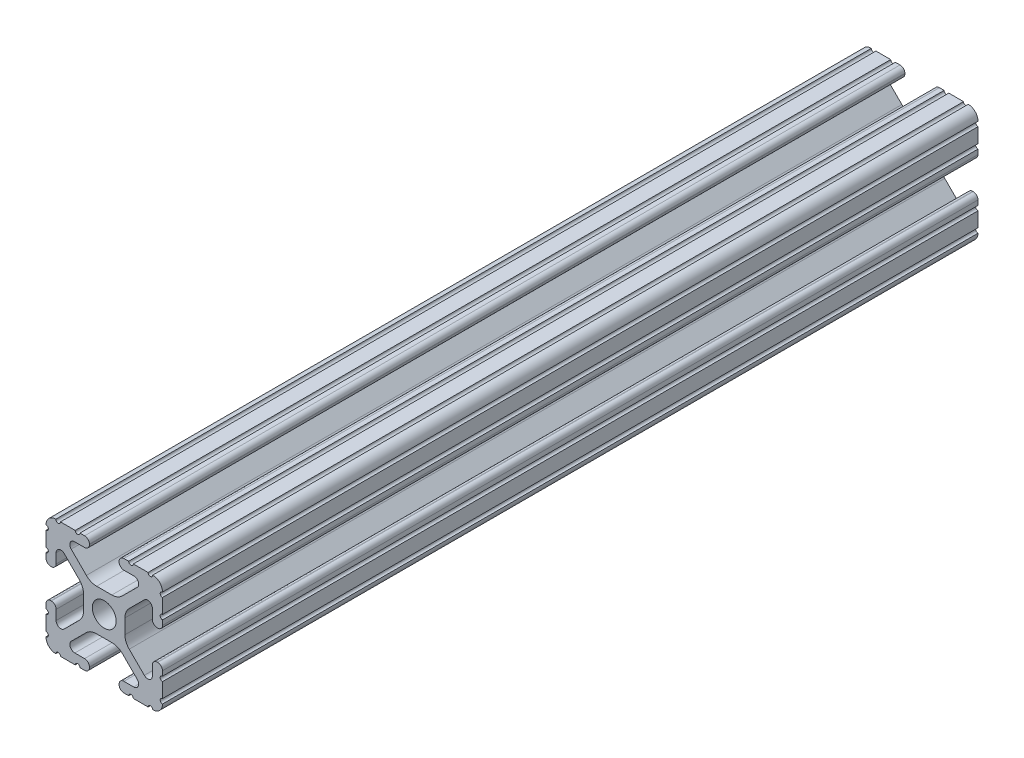
SolidWorks part; units mm, degrees
ref_plane "Front Plane" through (0, 0, 0) normal (0, 0, 1) x (1, 0, 0)
ref_plane "Top Plane" through (0, 0, 0) normal (0, 1, 0) x (1, 0, 0)
ref_plane "Right Plane" through (0, 0, 0) normal (1, 0, 0) x (0, 0, -1)
sketch "Sketch1" plane through (0, 0, 0) normal (0, 0, 1) x (1, 0, 0)
  line L0 (-1.7093, -4.4958) -> (1.7093, -4.4958)
  line L1 (3.9523, -5.4237) -> (7.1797, -8.6452)
  line L2 (6.4164, -10.4902) -> (4.2875, -10.4902)
  line L3 (3.2385, -11.5392) -> (3.2385, -11.651)
  line L4 (4.2875, -12.7) -> (5.3171, -12.7)
  line L5 (6.3331, -12.7) -> (9.5504, -12.7)
  line L6 (12.7, -9.5504) -> (12.7, -6.3331)
  line L7 (12.7, -5.3171) -> (12.7, -4.2875)
  line L8 (11.651, -3.2385) -> (11.5392, -3.2385)
  line L9 (10.4902, -4.2875) -> (10.4902, -6.4021)
  line L10 (8.7371, -7.1294) -> (5.441, -3.8408)
  line L11 (4.5085, -1.5932) -> (4.5085, 1.5932)
  line L12 (5.441, 3.8408) -> (8.7371, 7.1294)
  line L13 (10.4902, 6.4021) -> (10.4902, 4.2875)
  line L14 (11.5392, 3.2385) -> (11.651, 3.2385)
  line L15 (12.7, 4.2875) -> (12.7, 5.3171)
  line L16 (12.7, 6.3331) -> (12.7, 9.5504)
  line L17 (9.5504, 12.7) -> (6.3331, 12.7)
  line L18 (5.3171, 12.7) -> (4.2875, 12.7)
  line L19 (3.2385, 11.651) -> (3.2385, 11.5392)
  line L20 (4.2875, 10.4902) -> (6.4768, 10.4902)
  line L21 (7.207, 8.7244) -> (3.8983, 5.4232)
  line L22 (1.6558, 4.4958) -> (-1.6558, 4.4958)
  line L23 (-3.8983, 5.4232) -> (-7.207, 8.7244)
  line L24 (-6.4768, 10.4902) -> (-4.2875, 10.4902)
  line L25 (-3.2385, 11.5392) -> (-3.2385, 11.651)
  line L26 (-4.2875, 12.7) -> (-5.3171, 12.7)
  line L27 (-6.3331, 12.7) -> (-9.5504, 12.7)
  line L28 (-12.7, 9.5504) -> (-12.7, 6.3331)
  line L29 (-12.7, 5.3171) -> (-12.7, 4.2875)
  line L30 (-11.651, 3.2385) -> (-11.5392, 3.2385)
  line L31 (-10.4902, 4.2875) -> (-10.4902, 6.4021)
  line L32 (-8.7371, 7.1294) -> (-5.441, 3.8408)
  line L33 (-4.5085, 1.5932) -> (-4.5085, -1.5932)
  line L34 (-5.441, -3.8408) -> (-8.7371, -7.1294)
  line L35 (-10.4902, -6.4021) -> (-10.4902, -4.2875)
  line L36 (-11.5392, -3.2385) -> (-11.651, -3.2385)
  line L37 (-12.7, -4.2875) -> (-12.7, -5.3171)
  line L38 (-12.7, -6.3331) -> (-12.7, -9.5504)
  line L39 (-9.5504, -12.7) -> (-6.3331, -12.7)
  line L40 (-5.3171, -12.7) -> (-4.2875, -12.7)
  line L41 (-3.2385, -11.651) -> (-3.2385, -11.5392)
  line L42 (-4.2875, -10.4902) -> (-6.4164, -10.4902)
  line L43 (-7.1797, -8.6452) -> (-3.9523, -5.4237)
  line L44 (0, 0) -> (0, 2.5)
  line L45 (0, 0) -> (-2.5, 0)
  line L46 (0, 0) -> (0, -2.5)
  line L47 (0, 0) -> (2.5, 0)
  line L48 (0, 5) -> (0, 5.1035)
  line L49 (-5, 0) -> (-5.1035, 0)
  line L50 (0, -5) -> (0, -5.1035)
  line L51 (5, 0) -> (5.1035, 0)
  line L101 (-115.9492, 3668.6391) -> (-116.9788, 3668.6391)
  line L103 (-114.9001, 3668.6391) -> (-115.9492, 3668.6391)
  line L107 (-122.2281, 3668.6391) -> (-124.3615, 3668.6391)
  line L111 (-98.9618, 3668.6391) -> (-101.0952, 3668.6391)
  line L116 (-121.2121, 3668.6391) -> (-122.2281, 3668.6391)
  line L119 (-106.3445, 3668.6391) -> (-107.3741, 3668.6391)
  line L122 (-117.9948, 3668.6391) -> (-121.2121, 3668.6391)
  line L124 (-116.9788, 3668.6391) -> (-117.9948, 3668.6391)
  line L127 (-101.0952, 3668.6391) -> (-102.1112, 3668.6391)
  line L130 (-105.3285, 3668.6391) -> (-106.3445, 3668.6391)
  line L132 (-102.1112, 3668.6391) -> (-105.3285, 3668.6391)
  line L135 (-107.3741, 3668.6391) -> (-108.4231, 3668.6391)
  line L139 (-108.4231, 3668.6391) -> (-110.0059, 3668.6391)
  line L141 (-113.3174, 3668.6391) -> (-114.9001, 3668.6391)
  line L143 (-110.0059, 3668.6391) -> (-113.3174, 3668.6391)
  circle A0 centre (0, 0) radius 2.6035
  arc A1 (3.9523, -5.4237) -> (1.7093, -4.4958) centre (1.7093, -7.6708) ccw
  arc A2 (6.4164, -10.4902) -> (7.1797, -8.6452) centre (6.4164, -9.4098) ccw
  arc A3 (4.2875, -10.4902) -> (3.2385, -11.5392) centre (4.2875, -11.5392) ccw
  arc A4 (3.2385, -11.651) -> (4.2875, -12.7) centre (4.2875, -11.651) ccw
  arc A5 (6.3331, -12.7) -> (5.3171, -12.7) centre (5.8251, -12.7) ccw
  arc A6 (10.5664, -12.6998) -> (9.5504, -12.7) centre (10.0584, -12.7) ccw
  arc A7 (10.5664, -12.6998) -> (12.6998, -10.5664) centre (10.5918, -10.5918) ccw
  arc A8 (12.7, -9.5504) -> (12.6998, -10.5664) centre (12.7, -10.0584) ccw
  arc A9 (12.7, -5.3171) -> (12.7, -6.3331) centre (12.7, -5.8251) ccw
  arc A10 (12.7, -4.2875) -> (11.651, -3.2385) centre (11.651, -4.2875) ccw
  arc A11 (11.5392, -3.2385) -> (10.4902, -4.2875) centre (11.5392, -4.2875) ccw
  arc A12 (8.7371, -7.1294) -> (10.4902, -6.4021) centre (9.4628, -6.4021) ccw
  arc A13 (4.5085, -1.5932) -> (5.441, -3.8408) centre (7.6835, -1.5932) ccw
  arc A14 (5.441, 3.8408) -> (4.5085, 1.5932) centre (7.6835, 1.5932) ccw
  arc A15 (10.4902, 6.4021) -> (8.7371, 7.1294) centre (9.4628, 6.4021) ccw
  arc A16 (10.4902, 4.2875) -> (11.5392, 3.2385) centre (11.5392, 4.2875) ccw
  arc A17 (11.651, 3.2385) -> (12.7, 4.2875) centre (11.651, 4.2875) ccw
  arc A18 (12.7, 6.3331) -> (12.7, 5.3171) centre (12.7, 5.8251) ccw
  arc A19 (12.6998, 10.5664) -> (12.7, 9.5504) centre (12.7, 10.0584) ccw
  arc A20 (12.6998, 10.5664) -> (10.5664, 12.6998) centre (10.5918, 10.5918) ccw
  arc A21 (9.5504, 12.7) -> (10.5664, 12.6998) centre (10.0584, 12.7) ccw
  arc A22 (5.3171, 12.7) -> (6.3331, 12.7) centre (5.8251, 12.7) ccw
  arc A23 (4.2875, 12.7) -> (3.2385, 11.651) centre (4.2875, 11.651) ccw
  arc A24 (3.2385, 11.5392) -> (4.2875, 10.4902) centre (4.2875, 11.5392) ccw
  arc A25 (7.207, 8.7244) -> (6.4768, 10.4902) centre (6.4768, 9.4563) ccw
  arc A26 (1.6558, 4.4958) -> (3.8983, 5.4232) centre (1.6558, 7.6708) ccw
  arc A27 (-3.8983, 5.4232) -> (-1.6558, 4.4958) centre (-1.6558, 7.6708) ccw
  arc A28 (-6.4768, 10.4902) -> (-7.207, 8.7244) centre (-6.4768, 9.4563) ccw
  arc A29 (-4.2875, 10.4902) -> (-3.2385, 11.5392) centre (-4.2875, 11.5392) ccw
  arc A30 (-3.2385, 11.651) -> (-4.2875, 12.7) centre (-4.2875, 11.651) ccw
  arc A31 (-6.3331, 12.7) -> (-5.3171, 12.7) centre (-5.8251, 12.7) ccw
  arc A32 (-10.5664, 12.6998) -> (-9.5504, 12.7) centre (-10.0584, 12.7) ccw
  arc A33 (-10.5664, 12.6998) -> (-12.6998, 10.5664) centre (-10.5918, 10.5918) ccw
  arc A34 (-12.7, 9.5504) -> (-12.6998, 10.5664) centre (-12.7, 10.0584) ccw
  arc A35 (-12.7, 5.3171) -> (-12.7, 6.3331) centre (-12.7, 5.8251) ccw
  arc A36 (-12.7, 4.2875) -> (-11.651, 3.2385) centre (-11.651, 4.2875) ccw
  arc A37 (-11.5392, 3.2385) -> (-10.4902, 4.2875) centre (-11.5392, 4.2875) ccw
  arc A38 (-8.7371, 7.1294) -> (-10.4902, 6.4021) centre (-9.4628, 6.4021) ccw
  arc A39 (-4.5085, 1.5932) -> (-5.441, 3.8408) centre (-7.6835, 1.5932) ccw
  arc A40 (-5.441, -3.8408) -> (-4.5085, -1.5932) centre (-7.6835, -1.5932) ccw
  arc A41 (-10.4902, -6.4021) -> (-8.7371, -7.1294) centre (-9.4628, -6.4021) ccw
  arc A42 (-10.4902, -4.2875) -> (-11.5392, -3.2385) centre (-11.5392, -4.2875) ccw
  arc A43 (-11.651, -3.2385) -> (-12.7, -4.2875) centre (-11.651, -4.2875) ccw
  arc A44 (-12.7, -6.3331) -> (-12.7, -5.3171) centre (-12.7, -5.8251) ccw
  arc A45 (-12.6998, -10.5664) -> (-12.7, -9.5504) centre (-12.7, -10.0584) ccw
  arc A46 (-12.6998, -10.5664) -> (-10.5664, -12.6998) centre (-10.5918, -10.5918) ccw
  arc A47 (-9.5504, -12.7) -> (-10.5664, -12.6998) centre (-10.0584, -12.7) ccw
  arc A48 (-5.3171, -12.7) -> (-6.3331, -12.7) centre (-5.8251, -12.7) ccw
  arc A49 (-4.2875, -12.7) -> (-3.2385, -11.651) centre (-4.2875, -11.651) ccw
  arc A50 (-3.2385, -11.5392) -> (-4.2875, -10.4902) centre (-4.2875, -11.5392) ccw
  arc A51 (-7.1797, -8.6452) -> (-6.4164, -10.4902) centre (-6.4164, -9.4098) ccw
  arc A52 (-1.7093, -4.4958) -> (-3.9523, -5.4237) centre (-1.7093, -7.6708) ccw
extrude "Boss-Extrude1" add sketch "Sketch1" along normal blind 2463.8 contours A52 L0 A1 L1 A2 L2 A3 L3 A4 L4 A5 L5 A6 A7 A8 L6 A9 L7 A10 L8 A11 L9 A12 L10 A13 L11 A14 L12 A15 L13 A16 L14 A17 L15 A18 L16 A19 A20 A21 L17 A22 L18 A23 L19 A24 L20 A25 L21 A26 L22 A27
sketch "Sketch2" plane through (0, 0, 2463.8) normal (0, 0, 1) x (1, 0, 0)
  line L44 (-1.7093, -4.4958) -> (1.7093, -4.4958)
  line L45 (3.9523, -5.4237) -> (7.1797, -8.6452)
  line L46 (6.4164, -10.4902) -> (4.2875, -10.4902)
  line L47 (3.2385, -11.5392) -> (3.2385, -11.651)
  line L48 (4.2875, -12.7) -> (5.3171, -12.7)
  line L49 (6.3331, -12.7) -> (9.5504, -12.7)
  line L50 (12.7, -9.5504) -> (12.7, -6.3331)
  line L51 (12.7, -5.3171) -> (12.7, -4.2875)
  line L52 (11.651, -3.2385) -> (11.5392, -3.2385)
  line L53 (10.4902, -4.2875) -> (10.4902, -6.4021)
  line L54 (8.7371, -7.1294) -> (5.441, -3.8408)
  line L55 (4.5085, -1.5932) -> (4.5085, 1.5932)
  line L56 (5.441, 3.8408) -> (8.7371, 7.1294)
  line L57 (10.4902, 6.4021) -> (10.4902, 4.2875)
  line L58 (11.5392, 3.2385) -> (11.651, 3.2385)
  line L59 (12.7, 4.2875) -> (12.7, 5.3171)
  line L60 (12.7, 6.3331) -> (12.7, 9.5504)
  line L61 (9.5504, 12.7) -> (6.3331, 12.7)
  line L62 (5.3171, 12.7) -> (4.2875, 12.7)
  line L63 (3.2385, 11.651) -> (3.2385, 11.5392)
  line L64 (4.2875, 10.4902) -> (6.4768, 10.4902)
  line L65 (7.207, 8.7244) -> (3.8983, 5.4232)
  line L66 (1.6558, 4.4958) -> (-1.6558, 4.4958)
  line L67 (-3.8983, 5.4232) -> (-7.207, 8.7244)
  line L68 (-6.4768, 10.4902) -> (-4.2875, 10.4902)
  line L69 (-3.2385, 11.5392) -> (-3.2385, 11.651)
  line L70 (-4.2875, 12.7) -> (-5.3171, 12.7)
  line L71 (-6.3331, 12.7) -> (-9.5504, 12.7)
  line L72 (-12.7, 9.5504) -> (-12.7, 6.3331)
  line L73 (-12.7, 5.3171) -> (-12.7, 4.2875)
  line L74 (-11.651, 3.2385) -> (-11.5392, 3.2385)
  line L75 (-10.4902, 4.2875) -> (-10.4902, 6.4021)
  line L76 (-8.7371, 7.1294) -> (-5.441, 3.8408)
  line L77 (-4.5085, 1.5932) -> (-4.5085, -1.5932)
  line L78 (-5.441, -3.8408) -> (-8.7371, -7.1294)
  line L79 (-10.4902, -6.4021) -> (-10.4902, -4.2875)
  line L80 (-11.5392, -3.2385) -> (-11.651, -3.2385)
  line L81 (-12.7, -4.2875) -> (-12.7, -5.3171)
  line L82 (-12.7, -6.3331) -> (-12.7, -9.5504)
  line L83 (-9.5504, -12.7) -> (-6.3331, -12.7)
  line L84 (-5.3171, -12.7) -> (-4.2875, -12.7)
  line L85 (-3.2385, -11.651) -> (-3.2385, -11.5392)
  line L86 (-4.2875, -10.4902) -> (-6.4164, -10.4902)
  line L87 (-7.1797, -8.6452) -> (-3.9523, -5.4237)
  line L88 (-1.7093, -4.4958) -> (1.7093, -4.4958)
  line L89 (3.9523, -5.4237) -> (7.1797, -8.6452)
  line L90 (6.4164, -10.4902) -> (4.2875, -10.4902)
  line L91 (3.2385, -11.5392) -> (3.2385, -11.651)
  line L92 (4.2875, -12.7) -> (5.3171, -12.7)
  line L93 (6.3331, -12.7) -> (9.5504, -12.7)
  line L94 (12.7, -9.5504) -> (12.7, -6.3331)
  line L95 (12.7, -5.3171) -> (12.7, -4.2875)
  line L96 (11.651, -3.2385) -> (11.5392, -3.2385)
  line L97 (10.4902, -4.2875) -> (10.4902, -6.4021)
  line L98 (8.7371, -7.1294) -> (5.441, -3.8408)
  line L99 (4.5085, -1.5932) -> (4.5085, 1.5932)
  line L100 (5.441, 3.8408) -> (8.7371, 7.1294)
  line L101 (10.4902, 6.4021) -> (10.4902, 4.2875)
  line L102 (11.5392, 3.2385) -> (11.651, 3.2385)
  line L103 (12.7, 4.2875) -> (12.7, 5.3171)
  line L104 (12.7, 6.3331) -> (12.7, 9.5504)
  line L105 (9.5504, 12.7) -> (6.3331, 12.7)
  line L106 (5.3171, 12.7) -> (4.2875, 12.7)
  line L107 (3.2385, 11.651) -> (3.2385, 11.5392)
  line L108 (4.2875, 10.4902) -> (6.4768, 10.4902)
  line L109 (7.207, 8.7244) -> (3.8983, 5.4232)
  line L110 (1.6558, 4.4958) -> (-1.6558, 4.4958)
  line L111 (-3.8983, 5.4232) -> (-7.207, 8.7244)
  line L112 (-6.4768, 10.4902) -> (-4.2875, 10.4902)
  line L113 (-3.2385, 11.5392) -> (-3.2385, 11.651)
  line L114 (-4.2875, 12.7) -> (-5.3171, 12.7)
  line L115 (-6.3331, 12.7) -> (-9.5504, 12.7)
  line L116 (-12.7, 9.5504) -> (-12.7, 6.3331)
  line L117 (-12.7, 5.3171) -> (-12.7, 4.2875)
  line L118 (-11.651, 3.2385) -> (-11.5392, 3.2385)
  line L119 (-10.4902, 4.2875) -> (-10.4902, 6.4021)
  line L120 (-8.7371, 7.1294) -> (-5.441, 3.8408)
  line L121 (-4.5085, 1.5932) -> (-4.5085, -1.5932)
  line L122 (-5.441, -3.8408) -> (-8.7371, -7.1294)
  line L123 (-10.4902, -6.4021) -> (-10.4902, -4.2875)
  line L124 (-11.5392, -3.2385) -> (-11.651, -3.2385)
  line L125 (-12.7, -4.2875) -> (-12.7, -5.3171)
  line L126 (-12.7, -6.3331) -> (-12.7, -9.5504)
  line L127 (-9.5504, -12.7) -> (-6.3331, -12.7)
  line L128 (-5.3171, -12.7) -> (-4.2875, -12.7)
  line L129 (-3.2385, -11.651) -> (-3.2385, -11.5392)
  line L130 (-4.2875, -10.4902) -> (-6.4164, -10.4902)
  line L131 (-7.1797, -8.6452) -> (-3.9523, -5.4237)
  arc A52 (-1.7093, -4.4958) -> (-3.9523, -5.4237) centre (-1.7093, -7.6708) ccw
  arc A53 (3.9523, -5.4237) -> (1.7093, -4.4958) centre (1.7093, -7.6708) ccw
  arc A54 (6.4164, -10.4902) -> (7.1797, -8.6452) centre (6.4164, -9.4098) ccw
  arc A55 (4.2875, -10.4902) -> (3.2385, -11.5392) centre (4.2875, -11.5392) ccw
  arc A56 (3.2385, -11.651) -> (4.2875, -12.7) centre (4.2875, -11.651) ccw
  arc A57 (6.3331, -12.7) -> (5.3171, -12.7) centre (5.8251, -12.7) ccw
  arc A58 (10.5664, -12.6998) -> (9.5504, -12.7) centre (10.0584, -12.7) ccw
  arc A59 (10.5664, -12.6998) -> (12.6998, -10.5664) centre (10.5918, -10.5918) ccw
  arc A60 (12.7, -9.5504) -> (12.6998, -10.5664) centre (12.7, -10.0584) ccw
  arc A61 (12.7, -5.3171) -> (12.7, -6.3331) centre (12.7, -5.8251) ccw
  arc A62 (12.7, -4.2875) -> (11.651, -3.2385) centre (11.651, -4.2875) ccw
  arc A63 (11.5392, -3.2385) -> (10.4902, -4.2875) centre (11.5392, -4.2875) ccw
  arc A64 (8.7371, -7.1294) -> (10.4902, -6.4021) centre (9.4628, -6.4021) ccw
  arc A65 (4.5085, -1.5932) -> (5.441, -3.8408) centre (7.6835, -1.5932) ccw
  arc A66 (5.441, 3.8408) -> (4.5085, 1.5932) centre (7.6835, 1.5932) ccw
  arc A67 (10.4902, 6.4021) -> (8.7371, 7.1294) centre (9.4628, 6.4021) ccw
  arc A68 (10.4902, 4.2875) -> (11.5392, 3.2385) centre (11.5392, 4.2875) ccw
  arc A69 (11.651, 3.2385) -> (12.7, 4.2875) centre (11.651, 4.2875) ccw
  arc A70 (12.7, 6.3331) -> (12.7, 5.3171) centre (12.7, 5.8251) ccw
  arc A71 (12.6998, 10.5664) -> (12.7, 9.5504) centre (12.7, 10.0584) ccw
  arc A72 (12.6998, 10.5664) -> (10.5664, 12.6998) centre (10.5918, 10.5918) ccw
  arc A73 (9.5504, 12.7) -> (10.5664, 12.6998) centre (10.0584, 12.7) ccw
  arc A74 (5.3171, 12.7) -> (6.3331, 12.7) centre (5.8251, 12.7) ccw
  arc A75 (4.2875, 12.7) -> (3.2385, 11.651) centre (4.2875, 11.651) ccw
  arc A76 (3.2385, 11.5392) -> (4.2875, 10.4902) centre (4.2875, 11.5392) ccw
  arc A77 (7.207, 8.7244) -> (6.4768, 10.4902) centre (6.4768, 9.4563) ccw
  arc A78 (1.6558, 4.4958) -> (3.8983, 5.4232) centre (1.6558, 7.6708) ccw
  arc A79 (-3.8983, 5.4232) -> (-1.6558, 4.4958) centre (-1.6558, 7.6708) ccw
  arc A80 (-6.4768, 10.4902) -> (-7.207, 8.7244) centre (-6.4768, 9.4563) ccw
  arc A81 (-4.2875, 10.4902) -> (-3.2385, 11.5392) centre (-4.2875, 11.5392) ccw
  arc A82 (-3.2385, 11.651) -> (-4.2875, 12.7) centre (-4.2875, 11.651) ccw
  arc A83 (-6.3331, 12.7) -> (-5.3171, 12.7) centre (-5.8251, 12.7) ccw
  arc A84 (-10.5664, 12.6998) -> (-9.5504, 12.7) centre (-10.0584, 12.7) ccw
  arc A85 (-10.5664, 12.6998) -> (-12.6998, 10.5664) centre (-10.5918, 10.5918) ccw
  arc A86 (-12.7, 9.5504) -> (-12.6998, 10.5664) centre (-12.7, 10.0584) ccw
  arc A87 (-12.7, 5.3171) -> (-12.7, 6.3331) centre (-12.7, 5.8251) ccw
  arc A88 (-12.7, 4.2875) -> (-11.651, 3.2385) centre (-11.651, 4.2875) ccw
  arc A89 (-11.5392, 3.2385) -> (-10.4902, 4.2875) centre (-11.5392, 4.2875) ccw
  arc A90 (-8.7371, 7.1294) -> (-10.4902, 6.4021) centre (-9.4628, 6.4021) ccw
  arc A91 (-4.5085, 1.5932) -> (-5.441, 3.8408) centre (-7.6835, 1.5932) ccw
  arc A92 (-5.441, -3.8408) -> (-4.5085, -1.5932) centre (-7.6835, -1.5932) ccw
  arc A93 (-10.4902, -6.4021) -> (-8.7371, -7.1294) centre (-9.4628, -6.4021) ccw
  arc A94 (-10.4902, -4.2875) -> (-11.5392, -3.2385) centre (-11.5392, -4.2875) ccw
  arc A95 (-11.651, -3.2385) -> (-12.7, -4.2875) centre (-11.651, -4.2875) ccw
  arc A96 (-12.7, -6.3331) -> (-12.7, -5.3171) centre (-12.7, -5.8251) ccw
  arc A97 (-12.6998, -10.5664) -> (-12.7, -9.5504) centre (-12.7, -10.0584) ccw
  arc A98 (-12.6998, -10.5664) -> (-10.5664, -12.6998) centre (-10.5918, -10.5918) ccw
  arc A99 (-9.5504, -12.7) -> (-10.5664, -12.6998) centre (-10.0584, -12.7) ccw
  arc A100 (-5.3171, -12.7) -> (-6.3331, -12.7) centre (-5.8251, -12.7) ccw
  arc A101 (-4.2875, -12.7) -> (-3.2385, -11.651) centre (-4.2875, -11.651) ccw
  arc A102 (-3.2385, -11.5392) -> (-4.2875, -10.4902) centre (-4.2875, -11.5392) ccw
  arc A103 (-7.1797, -8.6452) -> (-6.4164, -10.4902) centre (-6.4164, -9.4098) ccw
  arc A104 (-1.7093, -4.4958) -> (-3.9523, -5.4237) centre (-1.7093, -7.6708) ccw
  arc A105 (3.9523, -5.4237) -> (1.7093, -4.4958) centre (1.7093, -7.6708) ccw
  arc A106 (6.4164, -10.4902) -> (7.1797, -8.6452) centre (6.4164, -9.4098) ccw
  arc A107 (4.2875, -10.4902) -> (3.2385, -11.5392) centre (4.2875, -11.5392) ccw
  arc A108 (3.2385, -11.651) -> (4.2875, -12.7) centre (4.2875, -11.651) ccw
  arc A109 (6.3331, -12.7) -> (5.3171, -12.7) centre (5.8251, -12.7) ccw
  arc A110 (10.5664, -12.6998) -> (9.5504, -12.7) centre (10.0584, -12.7) ccw
  arc A111 (10.5664, -12.6998) -> (12.6998, -10.5664) centre (10.5918, -10.5918) ccw
  arc A112 (12.7, -9.5504) -> (12.6998, -10.5664) centre (12.7, -10.0584) ccw
  arc A113 (12.7, -5.3171) -> (12.7, -6.3331) centre (12.7, -5.8251) ccw
  arc A114 (12.7, -4.2875) -> (11.651, -3.2385) centre (11.651, -4.2875) ccw
  arc A115 (11.5392, -3.2385) -> (10.4902, -4.2875) centre (11.5392, -4.2875) ccw
  arc A116 (8.7371, -7.1294) -> (10.4902, -6.4021) centre (9.4628, -6.4021) ccw
  arc A117 (4.5085, -1.5932) -> (5.441, -3.8408) centre (7.6835, -1.5932) ccw
  arc A118 (5.441, 3.8408) -> (4.5085, 1.5932) centre (7.6835, 1.5932) ccw
  arc A119 (10.4902, 6.4021) -> (8.7371, 7.1294) centre (9.4628, 6.4021) ccw
  arc A120 (10.4902, 4.2875) -> (11.5392, 3.2385) centre (11.5392, 4.2875) ccw
  arc A121 (11.651, 3.2385) -> (12.7, 4.2875) centre (11.651, 4.2875) ccw
  arc A122 (12.7, 6.3331) -> (12.7, 5.3171) centre (12.7, 5.8251) ccw
  arc A123 (12.6998, 10.5664) -> (12.7, 9.5504) centre (12.7, 10.0584) ccw
  arc A124 (12.6998, 10.5664) -> (10.5664, 12.6998) centre (10.5918, 10.5918) ccw
  arc A125 (9.5504, 12.7) -> (10.5664, 12.6998) centre (10.0584, 12.7) ccw
  arc A126 (5.3171, 12.7) -> (6.3331, 12.7) centre (5.8251, 12.7) ccw
  arc A127 (4.2875, 12.7) -> (3.2385, 11.651) centre (4.2875, 11.651) ccw
  arc A128 (3.2385, 11.5392) -> (4.2875, 10.4902) centre (4.2875, 11.5392) ccw
  arc A129 (7.207, 8.7244) -> (6.4768, 10.4902) centre (6.4768, 9.4563) ccw
  arc A130 (1.6558, 4.4958) -> (3.8983, 5.4232) centre (1.6558, 7.6708) ccw
  arc A131 (-3.8983, 5.4232) -> (-1.6558, 4.4958) centre (-1.6558, 7.6708) ccw
  arc A132 (-6.4768, 10.4902) -> (-7.207, 8.7244) centre (-6.4768, 9.4563) ccw
  arc A133 (-4.2875, 10.4902) -> (-3.2385, 11.5392) centre (-4.2875, 11.5392) ccw
  arc A134 (-3.2385, 11.651) -> (-4.2875, 12.7) centre (-4.2875, 11.651) ccw
  arc A135 (-6.3331, 12.7) -> (-5.3171, 12.7) centre (-5.8251, 12.7) ccw
  arc A136 (-10.5664, 12.6998) -> (-9.5504, 12.7) centre (-10.0584, 12.7) ccw
  arc A137 (-10.5664, 12.6998) -> (-12.6998, 10.5664) centre (-10.5918, 10.5918) ccw
  arc A138 (-12.7, 9.5504) -> (-12.6998, 10.5664) centre (-12.7, 10.0584) ccw
  arc A139 (-12.7, 5.3171) -> (-12.7, 6.3331) centre (-12.7, 5.8251) ccw
  arc A140 (-12.7, 4.2875) -> (-11.651, 3.2385) centre (-11.651, 4.2875) ccw
  arc A141 (-11.5392, 3.2385) -> (-10.4902, 4.2875) centre (-11.5392, 4.2875) ccw
  arc A142 (-8.7371, 7.1294) -> (-10.4902, 6.4021) centre (-9.4628, 6.4021) ccw
  arc A143 (-4.5085, 1.5932) -> (-5.441, 3.8408) centre (-7.6835, 1.5932) ccw
  arc A144 (-5.441, -3.8408) -> (-4.5085, -1.5932) centre (-7.6835, -1.5932) ccw
  arc A145 (-10.4902, -6.4021) -> (-8.7371, -7.1294) centre (-9.4628, -6.4021) ccw
  arc A146 (-10.4902, -4.2875) -> (-11.5392, -3.2385) centre (-11.5392, -4.2875) ccw
  arc A147 (-11.651, -3.2385) -> (-12.7, -4.2875) centre (-11.651, -4.2875) ccw
  arc A148 (-12.7, -6.3331) -> (-12.7, -5.3171) centre (-12.7, -5.8251) ccw
  arc A149 (-12.6998, -10.5664) -> (-12.7, -9.5504) centre (-12.7, -10.0584) ccw
  arc A150 (-12.6998, -10.5664) -> (-10.5664, -12.6998) centre (-10.5918, -10.5918) ccw
  arc A151 (-9.5504, -12.7) -> (-10.5664, -12.6998) centre (-10.0584, -12.7) ccw
  arc A152 (-5.3171, -12.7) -> (-6.3331, -12.7) centre (-5.8251, -12.7) ccw
  arc A153 (-4.2875, -12.7) -> (-3.2385, -11.651) centre (-4.2875, -11.651) ccw
  arc A154 (-3.2385, -11.5392) -> (-4.2875, -10.4902) centre (-4.2875, -11.5392) ccw
  arc A155 (-7.1797, -8.6452) -> (-6.4164, -10.4902) centre (-6.4164, -9.4098) ccw
  dimension "D1" = 0
extrude "Cut-Extrude1" cut sketch "Sketch2" against normal blind 2286
